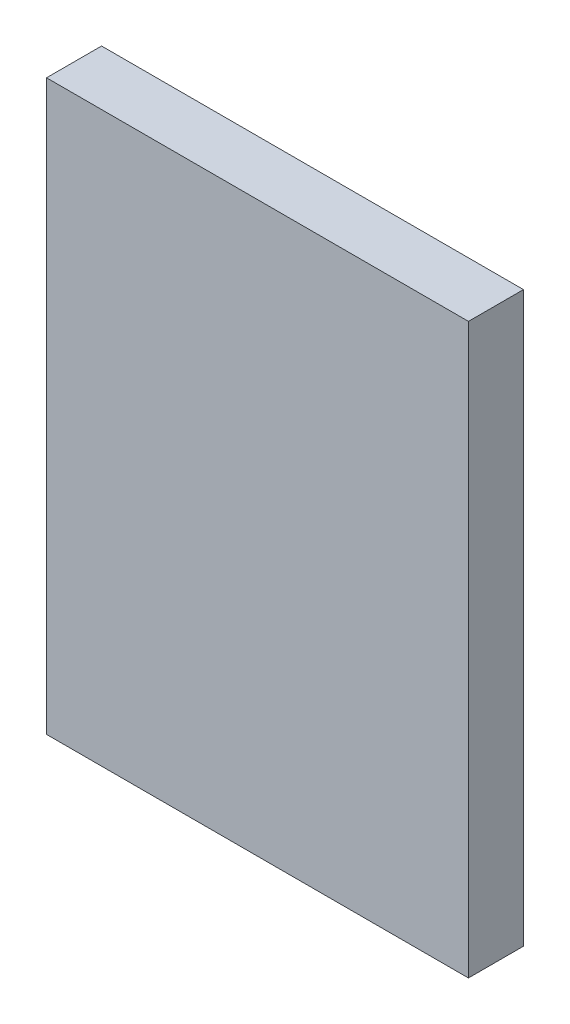
SolidWorks part; units mm, degrees
ref_plane "Plan de face" through (0, 0, 0) normal (0, 0, 1) x (1, 0, 0)
ref_plane "Plan de dessus" through (0, 0, 0) normal (0, 1, 0) x (1, 0, 0)
ref_plane "Plan de droite" through (0, 0, 0) normal (1, 0, 0) x (0, 0, -1)
sketch "Esquisse1" plane through (0, 0, 0) normal (0, 0, 1) x (1, 0, 0)
  line L1 (-11.5, 15.5) -> (11.5, 15.5)
  line L2 (-11.5, 15.5) -> (-11.5, -15.5)
  line L3 (-11.5, -15.5) -> (11.5, -15.5)
  line L4 (11.5, 15.5) -> (11.5, -15.5)
  line L5 (-11.5, 15.5) -> (11.5, -15.5) construction
  line L6 (-11.5, -15.5) -> (11.5, 15.5) construction
  point P0 (0, 0)
  dimension "D1" = 23
  dimension "D2" = 31
extrude "Boss.-Extru.1" add sketch "Esquisse1" along normal blind 3
